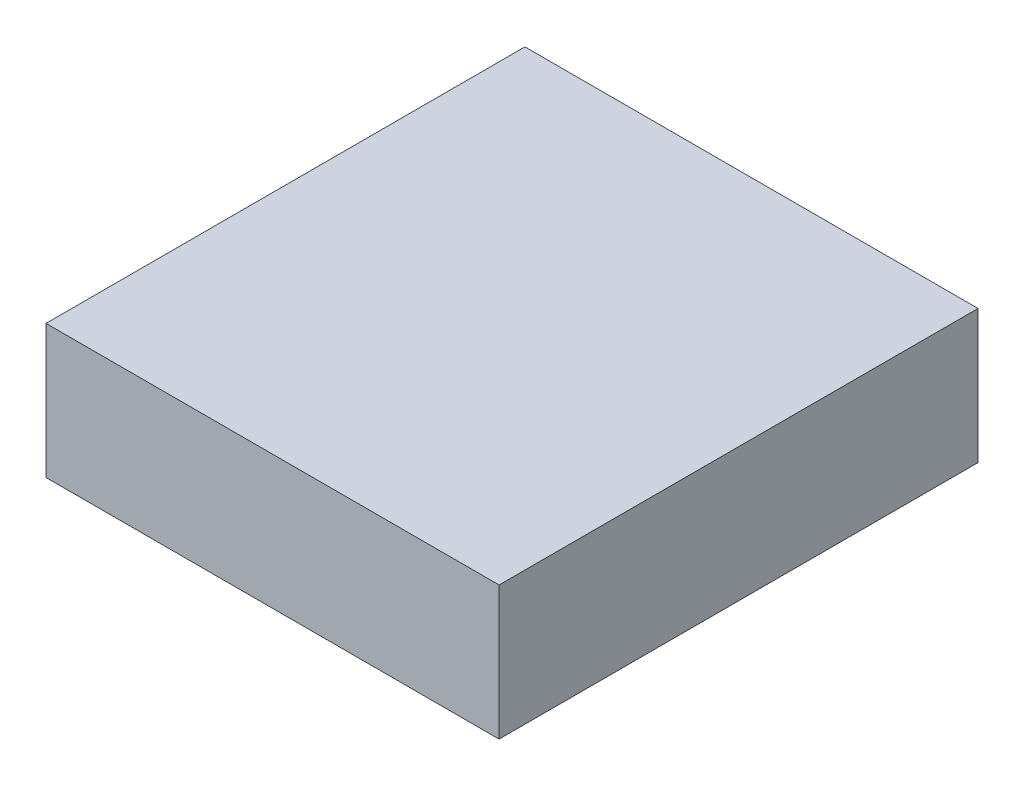
SolidWorks part; units mm, degrees
ref_plane "Front Plane" through (0, 0, 0) normal (0, 0, 1) x (1, 0, 0)
ref_plane "Top Plane" through (0, 0, 0) normal (0, 1, 0) x (1, 0, 0)
ref_plane "Right Plane" through (0, 0, 0) normal (1, 0, 0) x (0, 0, -1)
sketch "Sketch1" plane through (0, 0, 0) normal (0, 1, 0) x (1, 0, 0)
  line L1 (-64, 67.65) -> (0, 67.65)
  line L2 (-64, 67.65) -> (-64, 0)
  line L3 (-64, 0) -> (0, 0)
  line L4 (0, 67.65) -> (0, 0)
  dimension "D1" = 64
  dimension "D2" = 67.65
extrude "Boss-Extrude1" add sketch "Sketch1" along normal blind 18.86
